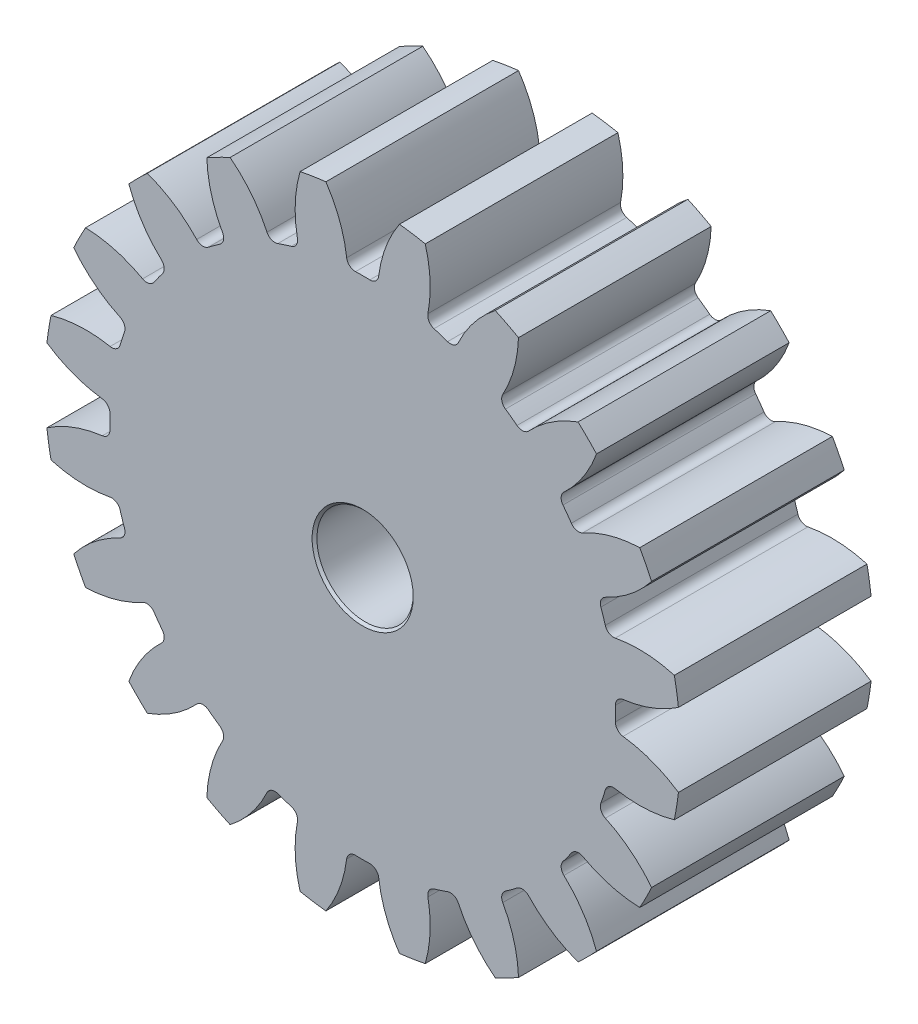
SolidWorks part; units mm, degrees
material "Plain Carbon Steel"
ref_plane "Front" through (0, 0, 0) normal (0, 0, 1) x (1, 0, 0)
ref_plane "Top" through (0, 0, 0) normal (0, 1, 0) x (1, 0, 0)
ref_plane "Right" through (0, 0, 0) normal (1, 0, 0) x (0, 0, -1)
sketch "Sketch1" plane through (0, 0, 0) normal (0, 0, 1) x (1, 0, 0)
  circle A0 centre (0, 0) radius 30
  circle A1 centre (0, 0) radius 33
  circle A2 centre (0, 0) radius 26.25
  dimension "D1" = 60
  dimension "D2" = 66
  dimension "D3" = 6.75
extrude "Extrude2" add sketch "Sketch1" along normal mid plane 20 contours A1
sketch "Sketch2" plane through (0, 0, 0) normal (0, 0, 1) x (1, 0, 0)
  line L0 (0, 0) -> (0, 33) construction
  line L1 (-2.3538, 29.9075) -> (2.3538, 29.9075) construction
  line L2 (0, 0) -> (-1.5844, 26.2021) construction
  line L3 (0, 23.4406) -> (-3.7671, 33.7907) construction
  line L4 (0, 0) -> (5.1623, 32.5937) construction
  line L5 (2.3538, 29.9075) -> (7.0034, 29.1711) construction
  circle A0 centre (0, 0) radius 33 construction
  arc A1 (-4.503, 33.7005) -> (-1.5844, 26.2021) centre (-14.7158, 25.4081) cw
  arc A2 (4.503, 33.7005) -> (1.5844, 26.2021) centre (14.7158, 25.4081) ccw
  circle A3 centre (0, 0) radius 26.25 construction
  arc A4 (1.5844, 26.2021) -> (-1.5844, 26.2021) centre (0, 0) ccw
  circle A5 centre (0, 0) radius 33 construction
  circle A7 centre (0, 0) radius 30 construction
  circle A8 centre (0, 0) radius 34
  arc A9 (4.503, 33.7005) -> (-4.503, 33.7005) centre (0, 0) ccw
  circle A10 centre (0, 0) radius 47.99 construction
  point P2 (0, 29.9075)
  point P15 (-10.6695, 53.4854)
  dimension "D4" = 95.98
  dimension "D2" = 20
  dimension "D3" = 9
  dimension "D1" = 1
extrude "Extrude3" cut sketch "Sketch2" against normal through all both and the other way through all
fillet "Fillet1" radius 0.9 2 edges at (1.5844, 26.2021, 0) (-1.5844, 26.2021, 0)
pattern_circular "CirPattern1" count 20 over 360 about axis through (0, 0, 0) along (0, 0, 1) of "Extrude3", "Fillet1"
sketch "Sketch3" plane through (0, 0, 10) normal (0, 0, 1) x (1, 0, 0)
  circle A0 centre (0, 0) radius 5
  dimension "D1" = 10
extrude "Extrude4" cut sketch "Sketch3" against normal through all both and the other way through all
chamfer "Chamfer1" distance 0.25 angle 45 2 edges at (5, 0, -10) (5, 0, 10)
scale "Scale1" scale about centroid uniform scaling yes scale factor 0.05
equation "\"Moduul\" = 3mm'Moduul"
equation "\"Aantal tanden\"= 20'Aantal tanden"
equation "\"D1@Sketch1\"=\"Aantal tanden\" * \"Moduul\""
equation "\"D2@Sketch1\"=(\"Aantal tanden\" + 2 ) * \"Moduul\""
equation "\"D3@Sketch1\"=\"Moduul\" * if( \"Moduul\"=>1.25,2.25,2.4)"
equation "\"D3@Sketch2\"=180 / \"Aantal tanden\""
equation "\"D1@Fillet1\"=0.3 * \"Moduul\""
equation "\"D1@CirPattern1\"=\"Aantal tanden\""
